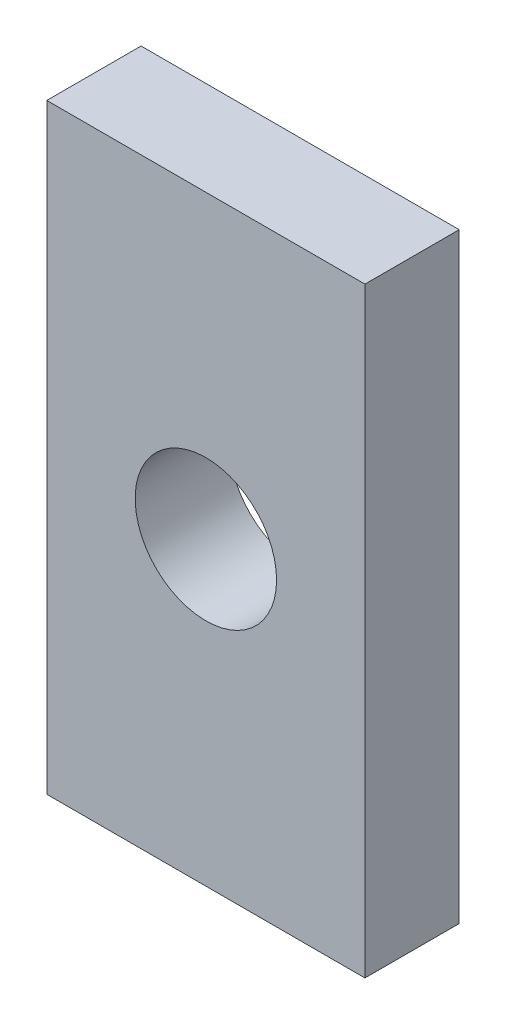
SolidWorks part; units mm, degrees
material "6061-T6 (SS)"
ref_plane "Alzado" through (0, 0, 0) normal (0, 0, 1) x (1, 0, 0)
ref_plane "Planta" through (0, 0, 0) normal (0, 1, 0) x (1, 0, 0)
ref_plane "Vista lateral" through (0, 0, 0) normal (1, 0, 0) x (0, 0, -1)
sketch "Sketch1" plane through (0, 0, 0) normal (0, 0, 1) x (1, 0, 0)
  line L1 (-20.25, 38.25) -> (20.25, 38.25)
  line L2 (-20.25, 38.25) -> (-20.25, -38.25)
  line L3 (-20.25, -38.25) -> (20.25, -38.25)
  line L4 (20.25, 38.25) -> (20.25, -38.25)
  line L5 (-20.25, 38.25) -> (20.25, -38.25) construction
  line L6 (-20.25, -38.25) -> (20.25, 38.25) construction
  point P0 (0, 0)
  dimension "D1" = 76.5
  dimension "D2" = 40.5
extrude "Boss-Extrude1" add sketch "Sketch1" along normal blind 12
sketch "Sketch2" plane through (0, 0, 12) normal (0, 0, 1) x (1, 0, 0)
  circle A0 centre (0, 0) radius 9
  dimension "D1" = 18
extrude "Cut-Extrude1" cut sketch "Sketch2" against normal up to next
